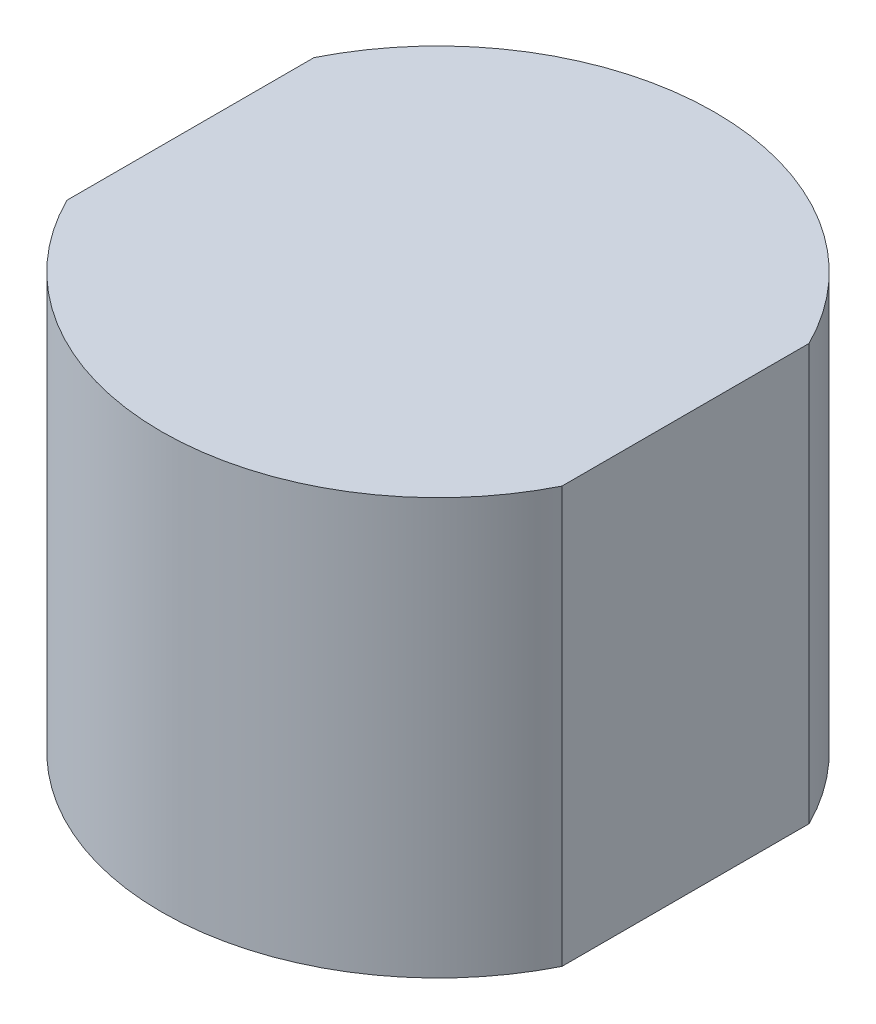
SolidWorks part; units mm, degrees
ref_plane "Front Plane" through (0, 0, 0) normal (0, 0, 1) x (1, 0, 0)
ref_plane "Top Plane" through (0, 0, 0) normal (0, 1, 0) x (1, 0, 0)
ref_plane "Right Plane" through (0, 0, 0) normal (1, 0, 0) x (0, 0, -1)
sketch "Sketch1" plane through (0, 0, 0) normal (0, 1, 0) x (1, 0, 0)
  line L0 (-5.9499, -2.97) -> (-5.9499, 2.97)
  line L1 (5.9499, -2.97) -> (5.9499, 2.97)
  circle A0 centre (0, 0) radius 6.65
  point P5 (0, 0)
  point P6 (0, 0)
extrude "Boss-Extrude1" add sketch "Sketch1" along normal blind 10 contours L1 A0 L0
